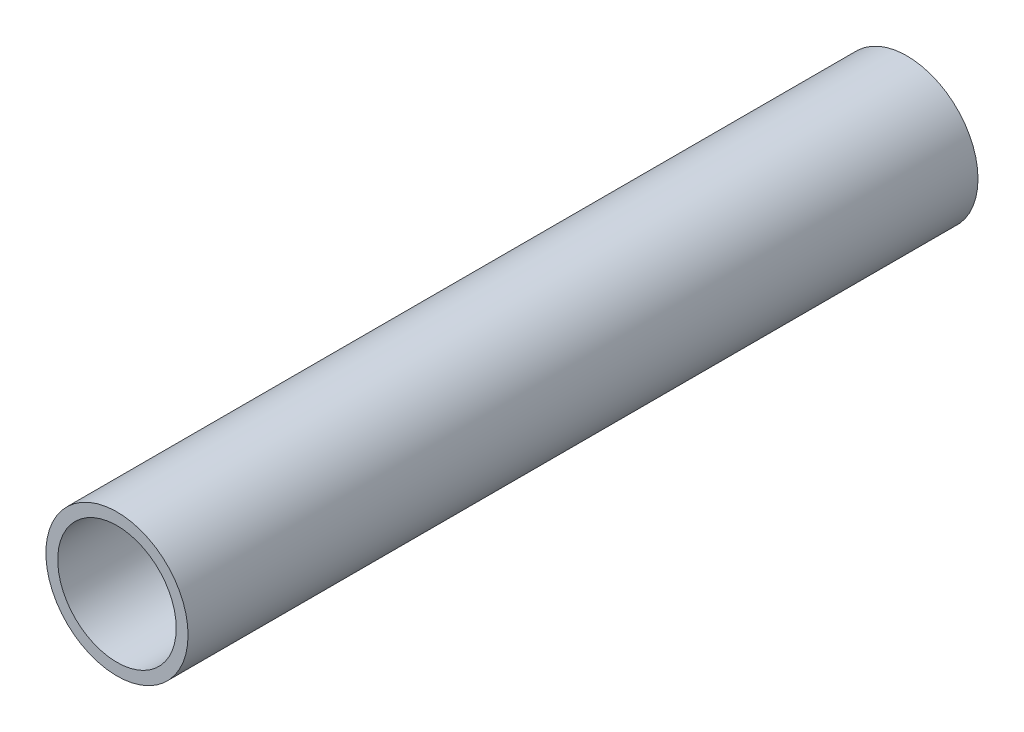
SolidWorks part; units mm, degrees
ref_plane "前视基准面" through (0, 0, 0) normal (0, 0, 1) x (1, 0, 0)
ref_plane "上视基准面" through (0, 0, 0) normal (0, 1, 0) x (1, 0, 0)
ref_plane "右视基准面" through (0, 0, 0) normal (1, 0, 0) x (0, 0, -1)
other "Configuration Table"
sketch "草图1" plane through (0, 0, 0) normal (0, 0, 1) x (1, 0, 0)
  circle A0 centre (0, 0) radius 9
  circle A1 centre (0, 0) radius 7.5
  dimension "D1" = 18
  dimension "D2" = 1.5
extrude "凸台-拉伸1" add sketch "草图1" along normal blind 100
